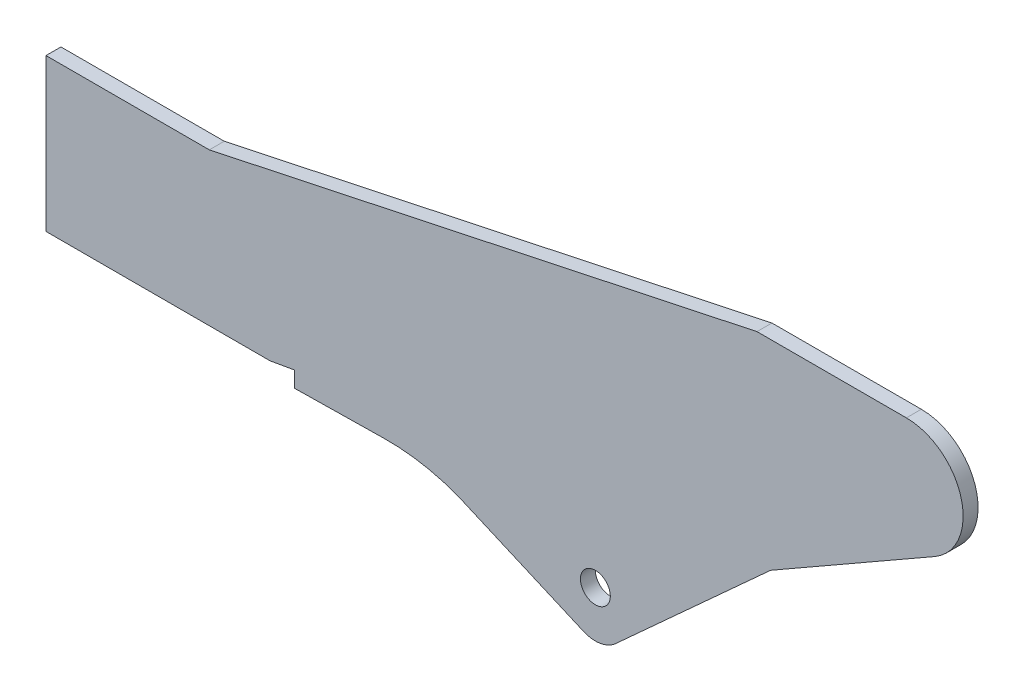
SolidWorks part; units mm, degrees
ref_plane "Front" through (0, 0, 0) normal (0, 0, 1) x (1, 0, 0)
ref_plane "Top" through (0, 0, 0) normal (0, 1, 0) x (1, 0, 0)
ref_plane "Right" through (0, 0, 0) normal (1, 0, 0) x (0, 0, -1)
sketch "Sketch2" plane through (0, 0, 0) normal (0, 0, 1) x (1, 0, 0)
  line L0 (0, 0) -> (164, 0)
  line L1 (164, 0) -> (714, 116.9061)
  line L2 (714, 116.9061) -> (864, 116.9061)
  line L3 (0, 0) -> (0, -153)
  line L4 (0, -153) -> (225, -153)
  line L5 (225, -153) -> (249.6202, -148.6588)
  line L6 (249.6202, -148.6588) -> (249.6202, -164.5888)
  line L7 (249.6202, -164.5888) -> (339.6202, -163.1893)
  line L8 (413.1421, -175.9698) -> (539.7511, -230.8711)
  line L9 (571.8722, -225.5403) -> (727.654, -83.8461)
  line L10 (727.654, -83.8461) -> (892.323, 10.4409)
  arc A0 (339.6202, -163.1893) -> (413.1421, -175.9698) centre (342.7298, -363.1651) cw
  arc A2 (539.7511, -230.8711) -> (571.8722, -225.5403) centre (551.6862, -203.3474) ccw
  arc A3 (892.323, 10.4409) -> (864, 116.9061) centre (864, 59.9061) ccw
  circle A4 centre (551.6862, -186.8334) radius 15
  point P19 (0, 0)
  dimension "D10" = 200
  dimension "D13" = 60
  dimension "D14" = 114
  dimension "D17" = 12.494
  dimension "D20" = 30
  dimension "D1" = 190
  dimension "D2" = 15.93
  dimension "D3" = 25
  dimension "D4" = 225
  dimension "D5" = 164
  dimension "D6" = 12
  dimension "D7" = 550
  dimension "D8" = 150
  dimension "D9" = 153
  dimension "D11" = 90
  dimension "D12" = 138
  dimension "D15" = 189.7523
  dimension "D16" = 210.5831
  dimension "D18" = 212.066
  dimension "D19" = 40.1581
  dimension "D21" = 16.514
extrude "Boss-Extrude1" add sketch "Sketch2" along normal mid plane 15
